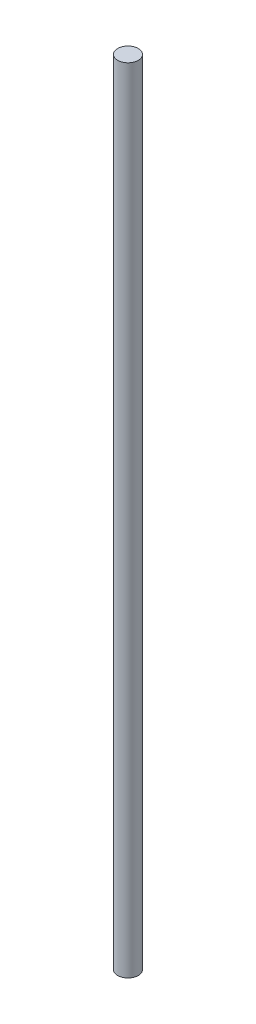
SolidWorks part; units mm, degrees
material "AISI 1010 Steel, hot rolled bar"
ref_plane "Front Plane" through (0, 0, 0) normal (0, 0, 1) x (1, 0, 0)
ref_plane "Top Plane" through (0, 0, 0) normal (0, 1, 0) x (1, 0, 0)
ref_plane "Right Plane" through (0, 0, 0) normal (1, 0, 0) x (0, 0, -1)
sketch "Sketch1" plane through (0, 0, 0) normal (0, 1, 0) x (1, 0, 0)
  circle A0 centre (0, 0) radius 5
  dimension "D1" = 10
extrude "Boss-Extrude1" add sketch "Sketch1" along normal mid plane 385
